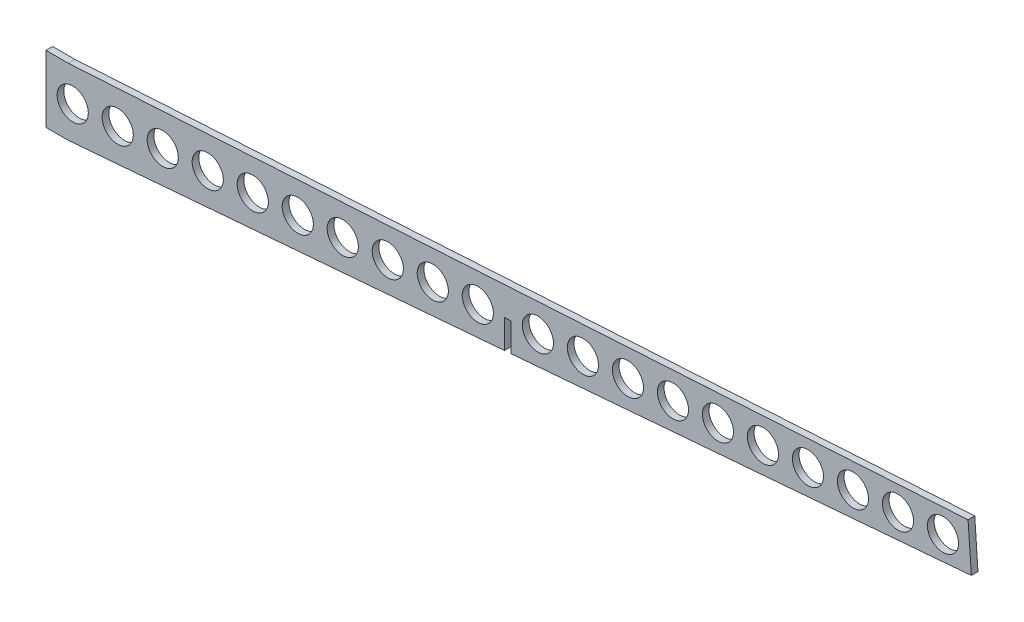
SolidWorks part; units mm, degrees
material "Pine"
ref_plane "Front Plane" through (0, 0, 0) normal (0, 0, 1) x (1, 0, 0)
ref_plane "Top Plane" through (0, 0, 0) normal (0, 1, 0) x (1, 0, 0)
ref_plane "Right Plane" through (0, 0, 0) normal (1, 0, 0) x (0, 0, -1)
sketch "Sketch1" plane through (0, 0, 0) normal (0, 0, 1) x (1, 0, 0)
  line L0 (-415, 15) -> (-405, 15) construction
  line L4 (-415, 0) -> (-415, 30)
  line L6 (-415, 30) -> (-405, 30)
  line L7 (-415, 0) -> (-405, 0)
  line L8 (-415, 0) -> (0, 0) construction
  line L9 (-415, 15) -> (0, 44.0196) construction
  line L10 (-0.7324, 54.494) -> (0.7324, 33.5452)
  line L11 (0, 44.0196) -> (0, 0) construction
  line L12 (-405, 30) -> (-0.7324, 54.494)
  line L13 (-405, 0) -> (0.7324, 33.5452)
  dimension "D1" = 30
  dimension "D2" = 10
  dimension "D3" = 415
  dimension "D4" = 4
  dimension "D5" = 21
extrude "Boss-Extrude1" add sketch "Sketch1" along normal blind 3
sketch "Sketch2" plane through (0, 0, 3) normal (0, 0, 1) x (1, 0, 0)
  line L0 (-415, 15) -> (-405, 15) construction
  line L1 (-415, 30) -> (-415, 0) construction
  line L2 (-405, 30) -> (-405, 15) construction
  line L3 (-405, 15) -> (0, 44.0196) construction
  line L4 (0.7324, 33.5452) -> (-0.7324, 54.494) construction
  line L5 (-415, 0) -> (0, 0) construction
  line L6 (-207.5, 0) -> (-207.5, 29.1515) construction
  line L7 (-209, 29.1515) -> (-206, 29.1515)
  line L8 (-209, 29.1515) -> (-209, 16.2049)
  line L9 (-405, 0) -> (0.7324, 33.5452) construction
  line L10 (-209, 16.2049) -> (-206, 16.2049)
  line L11 (-206, 16.2049) -> (-206, 29.1515)
  circle A1 centre (-403, 15.1433) radius 7
  circle A2 centre (-382.7778, 16.5923) radius 7
  circle A3 centre (-362.5556, 18.0413) radius 7
  circle A4 centre (-342.3333, 19.4903) radius 7
  circle A5 centre (-322.1111, 20.9393) radius 7
  circle A6 centre (-301.8889, 22.3883) radius 7
  circle A7 centre (-281.6667, 23.8373) radius 7
  circle A8 centre (-261.4444, 25.2862) radius 7
  circle A9 centre (-241.2222, 26.7352) radius 7
  circle A10 centre (-221, 28.1842) radius 7
  circle A11 centre (-194, 30.1189) radius 7
  circle A12 centre (-173.7778, 31.5679) radius 7
  circle A13 centre (-153.5556, 33.0168) radius 7
  circle A14 centre (-133.3333, 34.4658) radius 7
  circle A15 centre (-113.1111, 35.9148) radius 7
  circle A16 centre (-92.8889, 37.3638) radius 7
  circle A17 centre (-72.6667, 38.8128) radius 7
  circle A18 centre (-52.4444, 40.2618) radius 7
  circle A19 centre (-32.2222, 41.7108) radius 7
  circle A20 centre (-12, 43.1598) radius 7
  point P18 (-207.5, 29.1515)
  dimension "D3" = 14
  dimension "D5" = 12
  dimension "D6" = 14
  dimension "D1" = 3
  dimension "D2" = 12
  dimension "D7" = 12
  dimension "D9" = 12
  dimension "D4" = 10
  dimension "D8" = 10
extrude "Cut-Extrude1" cut sketch "Sketch2" against normal through all both and the other way through all
